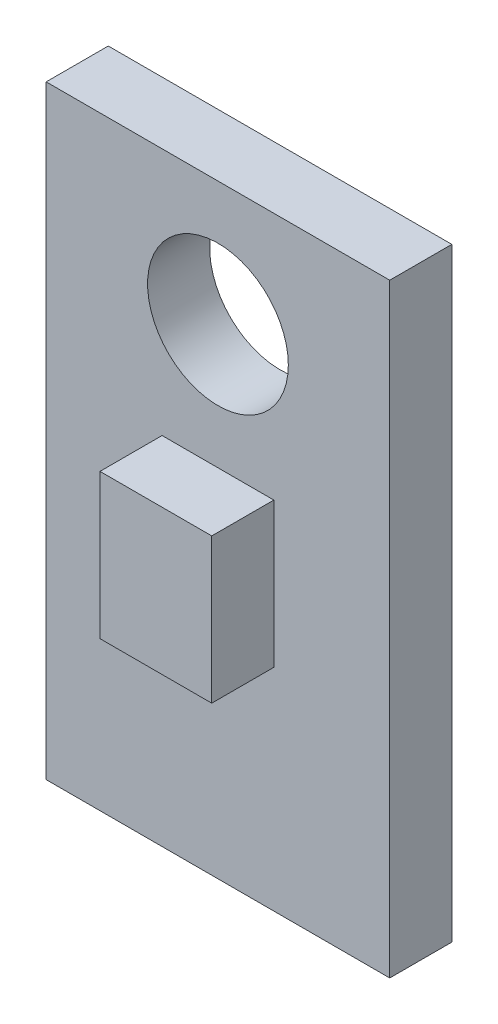
SolidWorks part; units mm, degrees
ref_plane "Front Plane" through (0, 0, 0) normal (0, 0, 1) x (1, 0, 0)
ref_plane "Top Plane" through (0, 0, 0) normal (0, 1, 0) x (1, 0, 0)
ref_plane "Right Plane" through (0, 0, 0) normal (1, 0, 0) x (0, 0, -1)
sketch "Sketch1" plane through (0, 0, 0) normal (0, 0, 1) x (1, 0, 0)
  line L1 (0, 0) -> (8.3, 0)
  line L2 (0, 0) -> (0, 14.6)
  line L3 (0, 14.6) -> (8.3, 14.6)
  line L4 (8.3, 0) -> (8.3, 14.6)
  dimension "D1" = 8.3
  dimension "D2" = 14.6
extrude "Boss-Extrude1" add sketch "Sketch1" along normal blind 1.5
sketch "Sketch2" plane through (0, 0, 1.5) normal (0, 0, 1) x (1, 0, 0)
  line L0 (4.15, 14.6) -> (4.15, 11.6) construction
  line L1 (8.3, 14.6) -> (0, 14.6) construction
  circle A0 centre (4.15, 11.6) radius 1.7
  dimension "D1" = 3.4
  dimension "D2" = 3
extrude "Cut-Extrude1" cut sketch "Sketch2" against normal blind 1.5
sketch "Sketch3" plane through (0, 0, 1.5) normal (0, 0, 1) x (1, 0, 0)
  line L0 (4.15, 5.1) -> (4.15, 0) construction
  line L1 (2.8, 8.6) -> (5.5, 8.6)
  line L2 (2.8, 8.6) -> (2.8, 5.1)
  line L3 (2.8, 5.1) -> (5.5, 5.1)
  line L4 (5.5, 8.6) -> (5.5, 5.1)
  line L5 (0, 0) -> (8.3, 0) construction
  line L6 (8.3, 14.6) -> (0, 14.6) construction
  dimension "D1" = 2.7
  dimension "D2" = 3.5
  dimension "D3" = 6
extrude "Boss-Extrude3" add sketch "Sketch3" along normal blind 1.5
